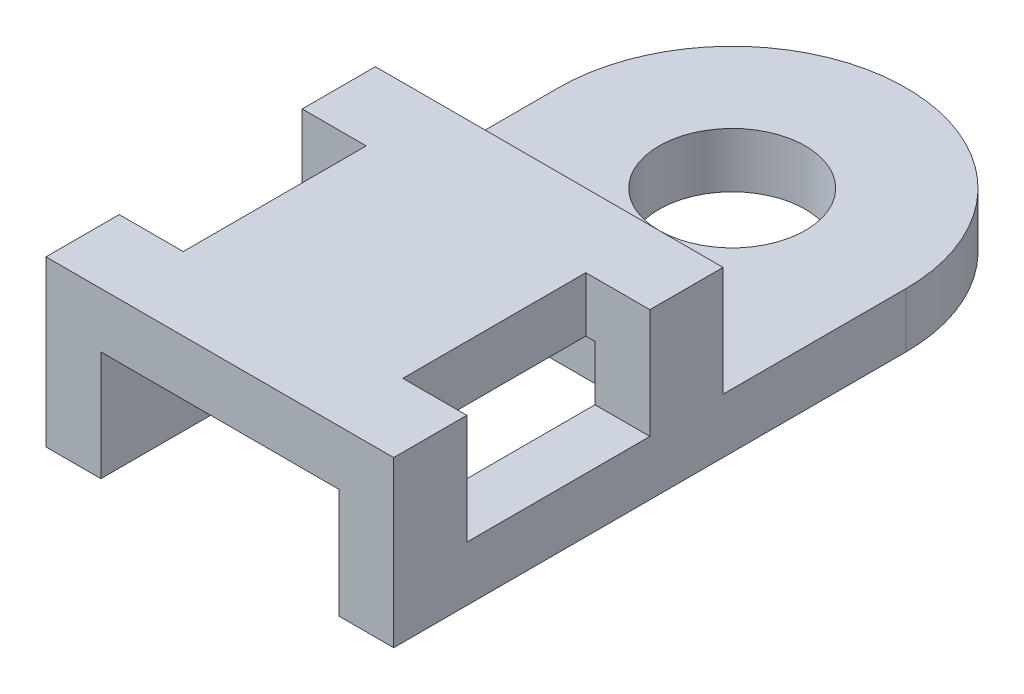
SolidWorks part; units mm, degrees
ref_plane "前视基准面" through (0, 0, 0) normal (0, 0, 1) x (1, 0, 0)
ref_plane "上视基准面" through (0, 0, 0) normal (0, 1, 0) x (1, 0, 0)
ref_plane "右视基准面" through (0, 0, 0) normal (1, 0, 0) x (0, 0, -1)
sketch "草图1" plane through (0, 0, 0) normal (0, 1, 0) x (1, 0, 0)
  line L0 (-4.75, 0) -> (-4.75, -14)
  line L1 (-4.75, -14) -> (4.75, -14)
  line L2 (4.75, -14) -> (4.75, 0)
  line L3 (-9.0124, 0) -> (11.9155, 0) construction
  circle A0 centre (0, 0) radius 2
  arc A1 (4.75, 0) -> (-4.75, 0) centre (0, 0) ccw
  point P10 (0, 0)
  point P11 (11.9155, 0)
  dimension "D1" = 4
  dimension "D2" = 9.5
  dimension "D3" = 14
extrude "凸台-拉伸1" add sketch "草图1" along normal blind 1.5
sketch "草图2" plane through (0, 1.5, 0) normal (0, 1, 0) x (1, 0, 0)
  line L0 (-4.75, -14) -> (4.75, -14)
  line L1 (4.75, -14) -> (4.75, -5)
  line L2 (4.75, -14) -> (4.75, 0) construction
  line L3 (4.75, -5) -> (-4.75, -5)
  line L4 (-4.75, 0) -> (-4.75, -14) construction
  line L5 (-4.75, -5) -> (-4.75, -14)
  dimension "D1" = 9
extrude "凸台-拉伸2" add sketch "草图2" along normal blind 3
sketch "草图3" plane through (0, 0, 0) normal (0, -1, 0) x (1, 0, 0)
  line L0 (3.25, 14) -> (3.25, 5)
  line L1 (-4.75, 14) -> (4.75, 14) construction
  line L2 (3.25, 5) -> (-3.25, 5)
  line L3 (-3.25, 5) -> (-3.25, 14)
  line L4 (-3.25, 14) -> (3.25, 14)
  line L6 (4.75, 14) -> (4.75, 0) construction
  line L7 (-4.75, 0) -> (-4.75, 14) construction
  dimension "D1" = 9
  dimension "D2" = 1.5
  dimension "D3" = 1.5
extrude "切除-拉伸1" cut sketch "草图3" against normal blind 3
sketch "草图4" plane through (0, 4.5, 0) normal (0, 1, 0) x (1, 0, 0)
  line L0 (-4.75, -7) -> (-3, -7)
  line L1 (-4.75, -5) -> (-4.75, -14) construction
  line L2 (-3, -7) -> (-3, -12)
  line L3 (-3, -12) -> (-4.75, -12)
  line L4 (-4.75, -12) -> (-4.75, -7)
  line L5 (0, 6.3129) -> (0, -20.2188) construction
  line L6 (-4.75, -14) -> (4.75, -14) construction
  line L7 (4.75, -12) -> (4.75, -7)
  line L8 (3, -12) -> (4.75, -12)
  line L9 (3, -7) -> (3, -12)
  line L10 (4.75, -7) -> (3, -7)
  dimension "D1" = 6
  dimension "D2" = 5
  dimension "D3" = 2
extrude "切除-拉伸2" cut sketch "草图4" against normal blind 3
